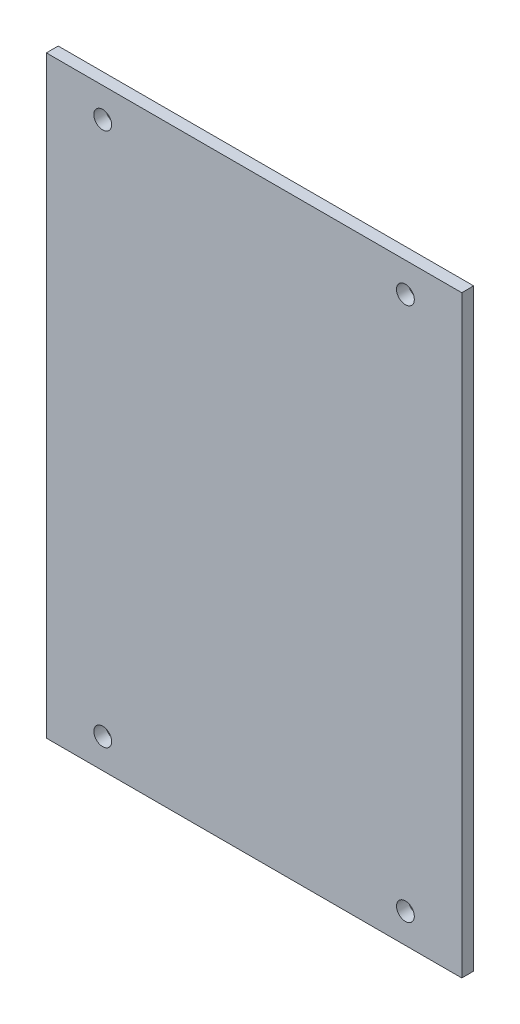
SolidWorks part; units mm, degrees
ref_plane "Front Plane" through (0, 0, 0) normal (0, 0, 1) x (1, 0, 0)
ref_plane "Top Plane" through (0, 0, 0) normal (0, 1, 0) x (1, 0, 0)
ref_plane "Right Plane" through (0, 0, 0) normal (1, 0, 0) x (0, 0, -1)
sketch "Sketch1" plane through (0, 0, 0) normal (0, 0, 1) x (1, 0, 0)
  line L0 (-25.5, 13) -> (-23.5, 11) construction
  line L1 (-25.5, -13) -> (25.5, -13)
  line L2 (-25.5, -13) -> (-25.5, 13)
  line L4 (25.5, -13) -> (25.5, 13)
  line L5 (0, 0) -> (0, 8.6449) construction
  line L6 (0, 0) -> (-7.1726, 0) construction
  line L7 (-25.5, 13) -> (-25.5, 17)
  line L9 (25.5, 17) -> (25.5, 13)
  line L10 (0, 30) -> (-7.1726, 30) construction
  line L11 (0, 30) -> (0, 21.3551) construction
  line L12 (-25.5, 17) -> (-23.5, 19) construction
  line L13 (25.5, 43) -> (25.5, 17)
  line L14 (-25.5, 43) -> (-25.5, 17)
  line L15 (-25.5, 43) -> (25.5, 43)
  circle A0 centre (-23.5, 11) radius 1
  circle A1 centre (-23.5, -11) radius 1
  circle A2 centre (23.5, -11) radius 1
  circle A3 centre (23.5, 11) radius 1
  circle A4 centre (23.5, 19) radius 1
  circle A5 centre (23.5, 41) radius 1
  circle A6 centre (-23.5, 41) radius 1
  circle A7 centre (-23.5, 19) radius 1
  point P0 (0, 0)
  point P34 (0, 30)
  dimension "D1" = 45
  dimension "D2" = 2.8284
extrude "Boss-Extrude1" add sketch "Sketch1" along normal blind 5
sketch "Sketch3" plane through (0, 0, 5) normal (0, 0, 1) x (1, 0, 0)
  line L1 (-25.5, 43) -> (25.5, 43)
  line L2 (-25.5, 43) -> (-25.5, -13)
  line L3 (-25.5, -13) -> (25.5, -13)
  line L4 (25.5, 43) -> (25.5, -13)
extrude "Boss-Extrude3" add sketch "Sketch3" along normal blind 2
ref_plane "Plane1" through (0, 15, 0) normal (0, -1, 0) x (-1, 0, 0)
sketch "Sketch7" plane through (0, 0, 7) normal (0, 0, 1) x (1, 0, 0)
  line L0 (-25.5, 43) -> (25.5, -13) construction
  line L1 (-35, -35) -> (35, -35)
  line L2 (-35, -35) -> (-35, 65)
  line L3 (35, -35) -> (35, 65)
  line L4 (-35, 65) -> (35, 65)
  line L5 (-35, -35) -> (35, 65) construction
  line L6 (35, -35) -> (-35, 65) construction
  line L7 (0, 15) -> (-28.5, 15) construction
  line L8 (0, 15) -> (0, -30) construction
  circle A0 centre (-25.5, -30) radius 1.5
  circle A1 centre (25.5, -30) radius 1.5
  circle A2 centre (25.5, 60) radius 1.5
  circle A3 centre (-25.5, 60) radius 1.5
  point P5 (0, 15)
  point P10 (0, 0)
extrude "Boss-Extrude5" add sketch "Sketch7" along normal blind 2
